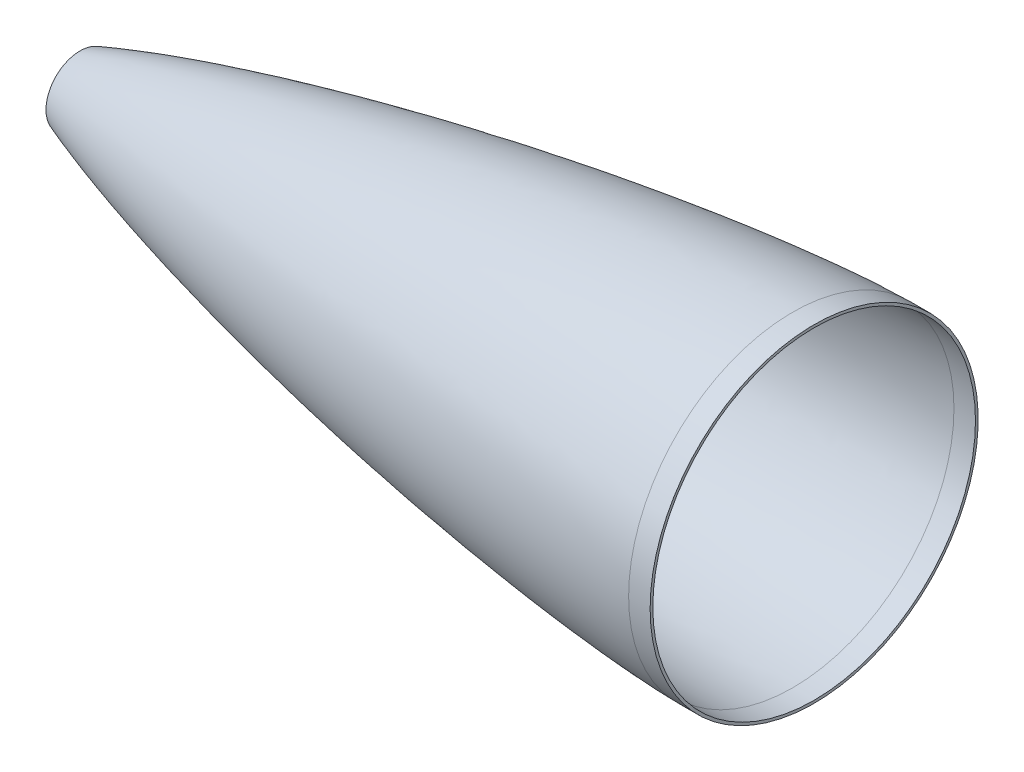
SolidWorks part; units mm, degrees
material "A-Glass Fiber"
ref_plane "Front Plane" through (0, 0, 0) normal (0, 0, 1) x (1, 0, 0)
ref_plane "Top Plane" through (0, 0, 0) normal (0, 1, 0) x (1, 0, 0)
ref_plane "Right Plane" through (0, 0, 0) normal (1, 0, 0) x (0, 0, -1)
sketch "Sketch1" plane through (0, 0, 0) normal (0, 0, 1) x (1, 0, 0)
  line L0 (0, 0) -> (457.2, 0) construction
  line L2 (457.2, 95.25) -> (457.2, 0) construction
  line L5 (457.2, 0) -> (469.8963, 0)
  line L7 (457.2, 95.25) -> (469.8963, 95.25)
  line L8 (469.8963, 0) -> (469.8963, 95.25) construction
  line L12 (457.1963, 96.8375) -> (471.4838, 96.8375) construction
  line L13 (457.1963, 96.8375) -> (469.8963, 96.8375)
  line L14 (469.8963, 96.8375) -> (469.8963, 95.25)
  line L15 (457.2, 0) -> (-1.613, 0) construction
  line L16 (471.4838, -1.5875) -> (471.4838, 96.8375) construction
  line L17 (457.2, 0) -> (0, 0) construction
  line L18 (457.2, -1.5875) -> (-1.8989, -1.5875) construction
  line L19 (457.2, -1.5875) -> (471.4838, -1.5875) construction
  line L20 (-1.613, 0) -> (0, 0)
  spline S0 degree 4 poles (0, 0) (0.0023, 0.0126) (0.0082, 0.0373) (0.0262, 0.085) (0.0706, 0.1767) (0.1354, 0.2842) (0.2204, 0.4066) (0.336, 0.5565) (0.5083, 0.7608) (0.8021, 1.0733) (1.3251, 1.5652) (2.2381, 2.3192) (3.8253, 3.4666) (6.614, 5.2253) (11.4561, 7.8766) (19.2936, 11.6017) (32.6156, 17.1305) (51.6883, 23.9819) (75.6131, 31.5462) (103.3102, 39.362) (131.8924, 46.6864) (160.6143, 53.4403) (189.4482, 59.6969) (218.3767, 65.4994) (247.3876, 70.874) (276.4727, 75.8318) (305.6259, 80.3722) (334.843, 84.4812) (364.1216, 88.1294) (389.7928, 90.8706) (411.8341, 92.8374) (428.9951, 94.0676) (440.0323, 94.6976) (448.6181, 95.062) (453.5214, 95.2002) (455.9737, 95.2443) (457.2, 95.25) knots 0 0 0 0 0 0.000108 0.000216 0.000433 0.000866 0.001175 0.001483 0.002044 0.003139 0.004822 0.007588 0.012112 0.019791 0.032854 0.05453 0.085907 0.142462 0.205216 0.267971 0.330725 0.393479 0.456233 0.518987 0.581741 0.644496 0.70725 0.770004 0.832758 0.895512 0.926889 0.958267 0.979133 0.989567 1 1 1 1 1 construction
  spline S1 degree 4 poles (0, 0) (0.0023, 0.0126) (0.0082, 0.0373) (0.0262, 0.085) (0.0706, 0.1767) (0.1354, 0.2842) (0.2204, 0.4066) (0.336, 0.5565) (0.5083, 0.7608) (0.8021, 1.0733) (1.3251, 1.5652) (2.2381, 2.3192) (3.8253, 3.4666) (6.614, 5.2253) (11.4561, 7.8766) (19.2936, 11.6017) (32.6156, 17.1305) (51.6883, 23.9819) (75.6131, 31.5462) (103.3102, 39.362) (131.8924, 46.6864) (160.6143, 53.4403) (189.4482, 59.6969) (218.3767, 65.4994) (247.3876, 70.874) (276.4727, 75.8318) (305.6259, 80.3722) (334.843, 84.4812) (364.1216, 88.1294) (389.7928, 90.8706) (411.8341, 92.8374) (428.9951, 94.0676) (440.0323, 94.6976) (448.6181, 95.062) (453.5214, 95.2002) (455.9737, 95.2443) (457.2, 95.25) knots 0 0 0 0 0 0.000108 0.000216 0.000433 0.000866 0.001175 0.001483 0.002044 0.003139 0.004822 0.007588 0.012112 0.019791 0.032854 0.05453 0.085907 0.142462 0.205216 0.267971 0.330725 0.393479 0.456233 0.518987 0.581741 0.644496 0.70725 0.770004 0.832758 0.895512 0.926889 0.958267 0.979133 0.989567 1 1 1 1 1
  spline S2 degree 1 poles (-1.8989, -1.5875) (457.1963, 96.8375) knots 0 0 1 1 construction
  spline S3 degree 3 poles (-1.8989, -1.5875) (-1.8716, -1.4358) (-1.8169, -1.1324) (-1.7486, -0.7532) (-1.694, -0.4498) (-1.6599, -0.2602) (-1.6326, -0.1085) (-1.6121, 0.0052) (-1.595, 0.1001) (-1.5814, 0.1758) (-1.5727, 0.2237) (-1.567, 0.2559) (-1.5636, 0.2739) (-1.5625, 0.2812) (-1.5411, 0.3918) (-1.5067, 0.5149) (-1.441, 0.6955) (-1.3886, 0.8061) (-1.3058, 0.9683) (-1.2132, 1.1209) (-1.0728, 1.3296) (-0.906, 1.5469) (-0.7105, 1.7767) (-0.5174, 1.9866) (-0.2609, 2.2487) (0.0592, 2.5515) (0.4443, 2.8898) (0.9608, 3.3175) (1.6111, 3.8178) (2.3999, 4.3829) (3.46, 5.0997) (4.801, 5.9446) (6.9705, 7.2185) (9.7204, 8.7026) (13.0595, 10.3683) (17.5542, 12.4746) (23.2313, 14.937) (30.1093, 17.7034) (37.0347, 20.3245) (43.9987, 22.8278) (53.3259, 26.0317) (65.0483, 29.8249) (79.1925, 34.1098) (93.3976, 38.1716) (107.6531, 42.042) (121.9511, 45.7433) (141.0645, 50.4743) (165.0378, 56.0378) (193.9118, 62.2237) (222.8767, 67.9595) (251.9217, 73.269) (281.0396, 78.1616) (310.2253, 82.6347) (339.4759, 86.6721) (368.79, 90.2401) (393.2717, 92.7732) (412.8919, 94.4772) (427.6244, 95.5657) (439.9241, 96.285) (449.7695, 96.6875) (454.7226, 96.8259) (457.1963, 96.8375) knots -0.004027 -0.004027 -0.004027 -0.004027 -0.003046 -0.002066 -0.001575 -0.001085 -0.00084 -0.000595 -0.00035 -0.000227 -0.000105 -0.000043 -0.000013 0.000003 0.000018 0.000079 0.000141 0.000263 0.000386 0.000631 0.000876 0.001366 0.001856 0.002347 0.002837 0.003817 0.004798 0.005778 0.007739 0.009701 0.011662 0.015584 0.019506 0.02735 0.035194 0.043038 0.058726 0.074414 0.090102 0.10579 0.121478 0.152854 0.18423 0.215606 0.246982 0.278358 0.309734 0.372486 0.435239 0.497991 0.560743 0.623495 0.686247 0.748999 0.811751 0.874504 0.90588 0.937256 0.968632 0.98432 1.000008 1.000008 1.000008 1.000008 only from (-1.613, 0) to (457.1963, 96.8375)
  dimension "D1" = 457.2
  dimension "D3" = 12.7
  dimension "D4" = 1.5875
revolve "Revolve3" add sketch "Sketch1" angle 360 about L0
ref_plane "Plane1" through (-1.613, 0, 0) normal (1, 0, 0) x (0, 0, -1)
sketch "Sketch2" plane through (-1.613, 0, 0) normal (1, 0, 0) x (0, 0, -1)
  circle A0 centre (0, 0) radius 96.8375 construction
  circle A1 centre (0, 0) radius 96.8375
extrude "Cut-Extrude1" cut sketch "Sketch2" along normal blind 38.1
